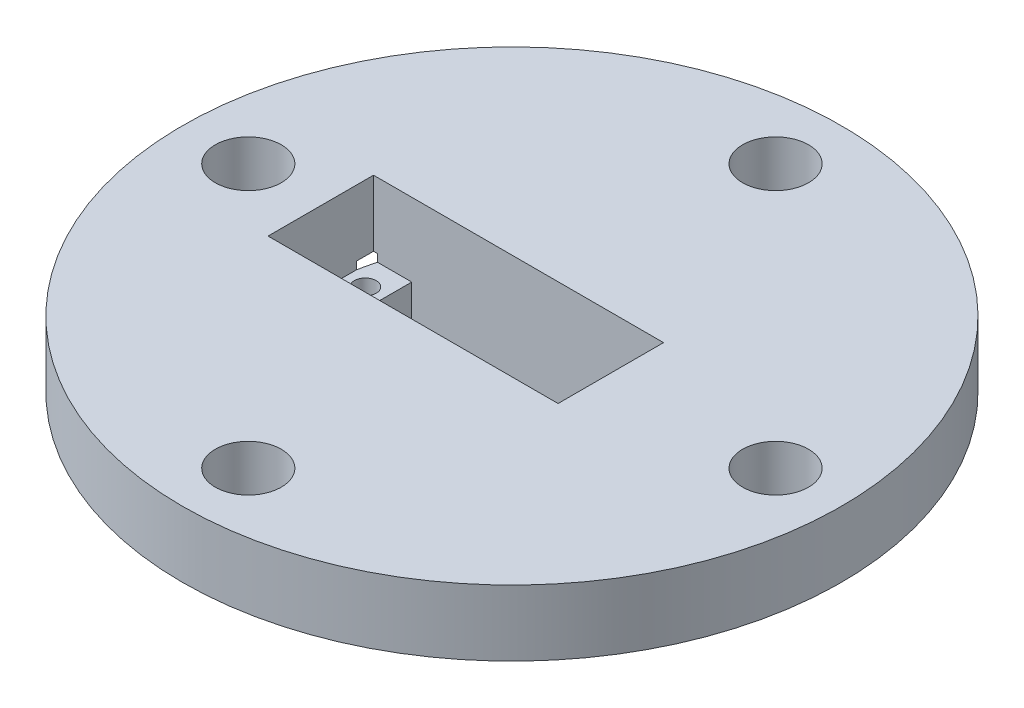
SolidWorks part; units mm, degrees
ref_plane "Front Plane" through (0, 0, 0) normal (0, 0, 1) x (1, 0, 0)
ref_plane "Top Plane" through (0, 0, 0) normal (0, 1, 0) x (1, 0, 0)
ref_plane "Right Plane" through (0, 0, 0) normal (1, 0, 0) x (0, 0, -1)
sketch "Sketch2" plane through (0, 0, 0) normal (0, 1, 0) x (1, 0, 0)
  circle A0 centre (0, 0) radius 63.5
  dimension "D1" = 127
extrude "Boss-Extrude1" add sketch "Sketch2" along normal blind 12.7 contours A0
sketch "Sketch3" plane through (0, 0, 0) normal (0, -1, 0) x (1, 0, 0)
  circle A0 centre (0, 50.8) radius 6.35
  circle A1 centre (-50.8, 0) radius 6.35
  circle A2 centre (0, -50.8) radius 6.35
  circle A3 centre (50.8, 0) radius 6.35
  dimension "D1" = 12.7
  dimension "D2" = 50.8
  dimension "D3" = 50.8
  dimension "D4" = 50.8
  dimension "D5" = 50.8
extrude "Cut-Extrude1" cut sketch "Sketch3" against normal through all contours A1
sketch "Sketch6" plane through (0, 0, 0) normal (0, -1, 0) x (1, 0, 0)
  line L1 (-36.83, 10.16) -> (19.05, 10.16)
  line L2 (-36.83, 10.16) -> (-36.83, -10.16)
  line L3 (-36.83, -10.16) -> (19.05, -10.16)
  line L4 (19.05, 10.16) -> (19.05, -10.16)
  point P4 (-36.83, 0)
  point P5 (19.05, 0)
  dimension "D1" = 55.88
  dimension "D2" = 20.32
  dimension "D3" = 19.05
extrude "Cut-Extrude3" cut sketch "Sketch6" against normal blind 27.686
sketch "Sketch8" plane through (0, 0, 0) normal (0, -1, 0) x (1, 0, 0)
  line L1 (-36.83, 10.16) -> (19.05, 10.16)
  line L2 (-36.83, 10.16) -> (-36.83, -10.16)
  line L3 (-36.83, -10.16) -> (19.05, -10.16)
  line L4 (19.05, 10.16) -> (19.05, -10.16)
  line L5 (-39.37, 17.78) -> (21.59, 17.78)
  line L6 (-39.37, 17.78) -> (-39.37, -17.78)
  line L7 (-39.37, -17.78) -> (21.59, -17.78)
  line L8 (21.59, 17.78) -> (21.59, -17.78)
  dimension "D1" = 7.62
  dimension "D2" = 7.62
  dimension "D3" = 2.54
  dimension "D4" = 2.54
extrude "Boss-Extrude2" add sketch "Sketch8" along normal up to vertex (1.45 mm away)
sketch "Sketch9" plane through (0, -1.45, 0) normal (0, -1, 0) x (1, 0, 0)
  line L0 (19.05, 10.16) -> (-36.83, 10.16) construction
  line L1 (-39.37, 17.78) -> (21.59, 17.78)
  line L2 (-39.37, 17.78) -> (-39.37, -17.78)
  line L3 (-39.37, -17.78) -> (21.59, -17.78)
  line L4 (21.59, 17.78) -> (21.59, -17.78)
  line L5 (-29.464, 10.16) -> (11.684, 10.16)
  line L6 (-29.464, 10.16) -> (-29.464, -10.16)
  line L7 (-29.464, -10.16) -> (11.684, -10.16)
  line L8 (11.684, 10.16) -> (11.684, -10.16)
  line L9 (-36.83, -10.16) -> (19.05, -10.16) construction
  circle A0 centre (-33.125, 4.875) radius 2.1058
  circle A1 centre (-33.125, -4.875) radius 2.1058
  circle A2 centre (15.475, 4.875) radius 2.1058
  circle A3 centre (15.475, -4.875) radius 2.1058
  dimension "D1" = 41.148
  dimension "D2" = 11.684
extrude "Boss-Extrude3" add sketch "Sketch9" along normal blind 10.16
sketch "Sketch11" plane through (0, 0, 0) normal (0, -1, 0) x (1, 0, 0)
  circle A0 centre (0, 0) radius 37.465
  circle A1 centre (0, 0) radius 63.5
  dimension "D1" = 74.93
  dimension "D2" = 127
extrude "Cut-Extrude5" cut sketch "Sketch11" along normal through all
